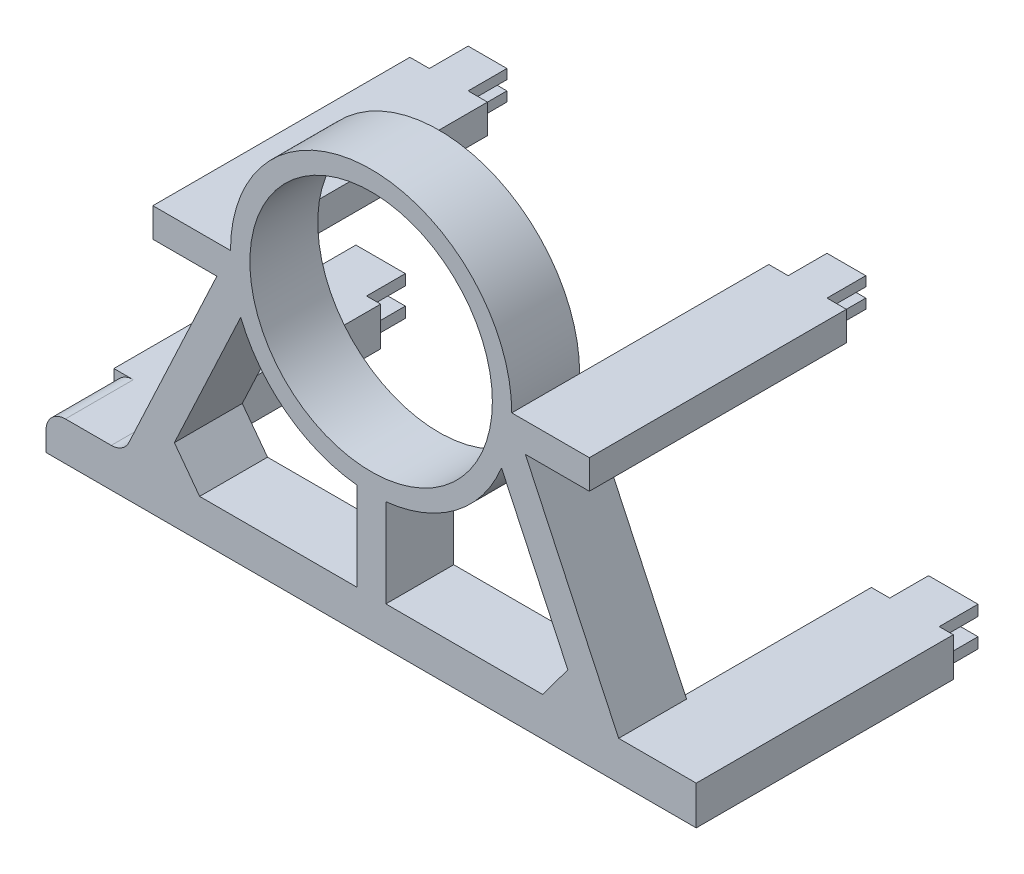
SolidWorks part; units mm, degrees
material "1023 Carbon Steel Sheet (SS)"
ref_plane "Ön Düzlem" through (0, 0, 0) normal (0, 0, 1) x (1, 0, 0)
ref_plane "Üst Düzlem" through (0, 0, 0) normal (0, 1, 0) x (1, 0, 0)
ref_plane "Sağ Düzlem" through (0, 0, 0) normal (1, 0, 0) x (0, 0, -1)
sketch "Sketch1" plane through (0, 0, 0) normal (0, 0, 1) x (1, 0, 0)
  line L0 (-72.5, 0) -> (-127.6009, -117.745)
  line L1 (-127.6009, -117.745) -> (-109.6009, -117.745)
  line L2 (-109.6009, -117.745) -> (-67.2156, -27.1719)
  line L3 (-109.6009, -117.745) -> (109.6009, -117.745)
  line L4 (0, -117.745) -> (0, -137.745)
  line L5 (167.6009, -137.745) -> (-167.6009, -137.745)
  line L6 (-167.6009, -137.745) -> (-167.6009, -117.745)
  line L7 (-167.6009, -117.745) -> (-127.6009, -117.745)
  line L8 (-7.4061, -72.1207) -> (-7.4061, -117.745)
  line L10 (7.5939, -72.1012) -> (7.5939, -117.745)
  line L11 (-101.4175, -100.2578) -> (-88.4083, -117.745)
  line L12 (-101.4175, -100.2578) -> (-119.4175, -100.2578)
  line L13 (101.4175, -100.2578) -> (119.4175, -100.2578)
  line L14 (101.4175, -100.2578) -> (88.4083, -117.745)
  line L15 (109.6009, -117.745) -> (67.2156, -27.1719)
  line L16 (72.5, 0) -> (127.6009, -117.745)
  line L17 (167.6009, -137.745) -> (167.6009, -117.745)
  line L18 (167.6009, -117.745) -> (127.6009, -117.745)
  line L19 (127.6009, -117.745) -> (109.6009, -117.745)
  line L20 (7.4061, -72.1207) -> (7.4061, -117.745)
  circle A0 centre (0, 0) radius 62.5
  circle A1 centre (0, 0) radius 72.5
  dimension "D1" = 125
  dimension "D2" = 10
  dimension "D3" = 100
  dimension "D4" = 130
  dimension "D5" = 18
  dimension "D6" = 40
  dimension "D7" = 167.6009
  dimension "D8" = 15
  dimension "D9" = 20
  dimension "D10" = 45.6243
  dimension "D11" = 21.7955
  dimension "D12" = 17.4872
extrude "Boss-Extrude8" add sketch "Sketch1" along normal blind 35 contours A1 A0 | A1 L0 L12 L2 | L2 L12 L0 L1 | L11 L2 L3 | L7 L6 L5 L4 L3 L1 | L18 L19 L3 L4 L5 L17 | L3 L15 L14 | L19 L16 L13 L15 | A1 L15 L13 L16
sketch "Sketch2" plane through (0, -117.745, 0) normal (0, 1, 0) x (1, 0, 0)
  line L0 (-7.4061, 0) -> (-7.4061, -35)
  line L1 (-88.4083, -35) -> (88.4083, -35) construction
  line L2 (-7.4061, 0) -> (7.5939, 0)
  line L3 (7.5939, 0) -> (7.5939, -35)
  line L4 (7.5939, -35) -> (-7.4061, -35)
extrude "Boss-Extrude9" add sketch "Sketch2" along normal up to surface (45.6243 mm away)
fillet "Fillet4" radius 10 1 edges at (-167.6009, -117.745, 17.5)
fillet "Fillet5" radius 10 1 edges at (-127.6009, -117.745, 17.5)
ref_plane "Plane3" through (72.5, 0, 0) normal (1, 0, 0) x (0, 0, -1)
sketch "Sketch6" plane through (72.5, 0, 0) normal (1, 0, 0) x (0, 0, -1)
  line L0 (19.25, 0) -> (-19.25, 0) construction
  line L1 (-35, 0) -> (0, 0)
  line L2 (-35, 0) -> (-35, -15)
  line L3 (-35, -15) -> (0, -15)
  line L4 (0, 0) -> (0, -15)
  line L5 (-35, 72.5) -> (-35, 0) construction
  line L6 (0, 72.5) -> (0, -72.5) construction
  dimension "D1" = 35
  dimension "D2" = 15
ref_plane "Plane5" through (-72.5, 0, 0) normal (1, 0, 0) x (0, 0, -1)
sketch "Sketch10" plane through (-72.5, 0, 0) normal (1, 0, 0) x (0, 0, -1)
  line L0 (-35, 0) -> (-35, -111.9835) construction
  line L1 (0, 0) -> (-35, 0)
  line L2 (0, 0) -> (0, -15)
  line L3 (0, -15) -> (-35, -15)
  line L4 (-35, 0) -> (-35, -15)
  dimension "D1" = 35
  dimension "D2" = 15
extrude "Boss-Extrude12" add sketch "Sketch10" against normal blind 40
extrude "Boss-Extrude10" add sketch "Sketch6" along normal blind 40
sketch "Sketch12" plane through (0, 0, 0) normal (0, 0, -1) x (-1, 0, 0)
  line L4 (-167.6009, -137.745) -> (-125.3715, -137.745)
  line L5 (-167.6009, -137.745) -> (167.6009, -137.745) construction
  line L6 (-125.3715, -137.745) -> (-125.3715, -117.745)
  line L7 (-127.6009, -117.745) -> (-109.6009, -117.745) construction
  line L8 (-125.3715, -117.745) -> (-167.6009, -117.745)
  line L9 (-167.6009, -117.745) -> (-167.6009, -137.745)
  line L14 (127.6009, -117.745) -> (127.6009, -137.745)
  line L15 (127.6009, -137.745) -> (167.6009, -137.745)
  line L16 (167.6009, -137.745) -> (167.6009, -117.745)
  line L17 (167.6009, -117.745) -> (127.6009, -117.745)
  line L18 (-112.5, 0) -> (-72.5, 0)
  line L19 (-72.5, 0) -> (-72.5, -15)
  line L20 (-72.5, -15) -> (-112.5, -15)
  line L21 (-112.5, -15) -> (-112.5, 0)
  line L23 (112.5, 0) -> (72.5042, 0)
  line L24 (112.5, 0) -> (112.5, -15)
  line L25 (112.5, -15) -> (72.5042, -15)
  line L26 (72.5042, 0) -> (72.5042, -15)
  dimension "D1" = 20
  dimension "D2" = 42.2294
  dimension "D3" = 15
  dimension "D4" = 40
  dimension "D5" = 15
  dimension "D6" = 39.9958
extrude "Boss-Extrude13" add sketch "Sketch12" along normal blind 97.5
sketch "Sketch13" plane through (0, 0, -97.5) normal (0, 0, -1) x (-1, 0, 0)
  line L0 (-72.5, 0) -> (-112.5, 0) construction
  line L1 (-102.5, 0) -> (-82.5, 0)
  line L2 (-102.5, 0) -> (-102.5, -5)
  line L3 (-102.5, -5) -> (-82.5, -5)
  line L4 (-82.5, 0) -> (-82.5, -5)
  line L5 (-112.5, -15) -> (-72.5, -15) construction
  line L6 (-102.5, -15) -> (-82.5, -15)
  line L7 (-102.5, -15) -> (-102.5, -10)
  line L8 (-102.5, -10) -> (-82.5, -10)
  line L9 (-82.5, -15) -> (-82.5, -10)
  line L10 (112.5, 0) -> (72.5042, 0) construction
  line L11 (82.5, 0) -> (102.5, 0)
  line L12 (82.5, 0) -> (82.5, -5)
  line L13 (82.5, -5) -> (102.5, -5)
  line L14 (102.5, 0) -> (102.5, -5)
  line L15 (72.5042, -15) -> (112.5, -15) construction
  line L16 (82.5, -15) -> (102.5, -15)
  line L17 (82.5, -15) -> (82.5, -10)
  line L18 (82.5, -10) -> (102.5, -10)
  line L19 (102.5, -15) -> (102.5, -10)
  line L20 (167.6009, -117.745) -> (127.6009, -117.745) construction
  line L21 (134.8509, -117.745) -> (160.3509, -117.745)
  line L22 (134.8509, -117.745) -> (134.8509, -123.245)
  line L23 (134.8509, -123.245) -> (160.3509, -123.245)
  line L24 (160.3509, -117.745) -> (160.3509, -123.245)
  line L25 (-167.6009, -137.745) -> (167.6009, -137.745) construction
  line L26 (134.8509, -137.745) -> (160.3509, -137.745)
  line L27 (134.8509, -137.745) -> (134.8509, -132.245)
  line L28 (134.8509, -132.245) -> (160.3509, -132.245)
  line L29 (160.3509, -137.745) -> (160.3509, -132.245)
  line L30 (-167.6009, -117.745) -> (-127.6009, -117.745) construction
  line L31 (-160.3509, -117.745) -> (-134.8509, -117.745)
  line L32 (-160.3509, -117.745) -> (-160.3509, -123.245)
  line L33 (-160.3509, -123.245) -> (-134.8509, -123.245)
  line L34 (-134.8509, -117.745) -> (-134.8509, -123.245)
  line L35 (-112.5, 0) -> (-112.5, -15) construction
  line L36 (-160.3509, -137.745) -> (-134.8509, -137.745)
  line L37 (-160.3509, -137.745) -> (-160.3509, -132.245)
  line L38 (-160.3509, -132.245) -> (-134.8509, -132.245)
  line L39 (-134.8509, -137.745) -> (-134.8509, -132.245)
  dimension "D1" = 20
  dimension "D2" = 10
  dimension "D3" = 5
  dimension "D4" = 5
  dimension "D5" = 20
  dimension "D6" = 10
  dimension "D7" = 10
  dimension "D8" = 20
  dimension "D9" = 5
  dimension "D10" = 5
  dimension "D11" = 10
  dimension "D12" = 20
  dimension "D13" = 7.25
  dimension "D14" = 25.5
  dimension "D15" = 5.5
  dimension "D16" = 5.5
  dimension "D17" = 25.5
  dimension "D18" = 7.25
  dimension "D19" = 7.25
  dimension "D20" = 7.25
  dimension "D21" = 25.5
  dimension "D22" = 25.5
  dimension "D23" = 5.5
  dimension "D24" = 5.5
extrude "Boss-Extrude14" add sketch "Sketch13" along normal blind 20
